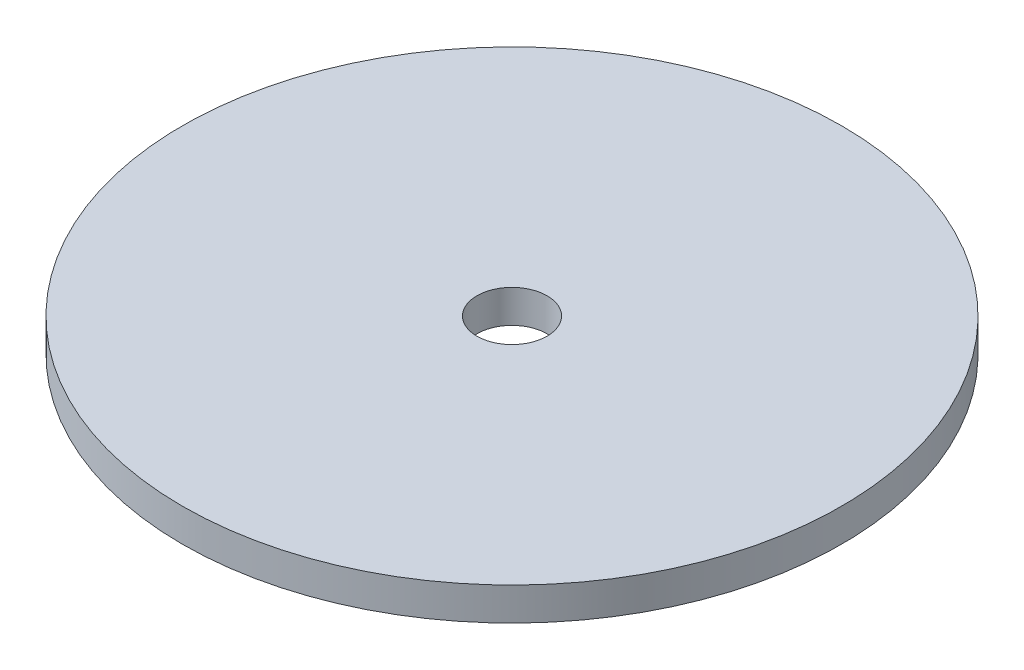
SolidWorks part; units mm, degrees
ref_plane "Front Plane" through (0, 0, 0) normal (0, 0, 1) x (1, 0, 0)
ref_plane "Top Plane" through (0, 0, 0) normal (0, 1, 0) x (1, 0, 0)
ref_plane "Right Plane" through (0, 0, 0) normal (1, 0, 0) x (0, 0, -1)
sketch "Sketch1" plane through (0, 0, 0) normal (0, 1, 0) x (1, 0, 0)
  circle A0 centre (0, 0) radius 31.75
  dimension "D1" = 63.5
extrude "Boss-Extrude1" add sketch "Sketch1" along normal mid plane 3.175
sketch "Sketch2" plane through (0, 1.5875, 0) normal (0, 1, 0) x (1, 0, 0)
  circle A2 centre (0, 0) radius 3.3782
  point P1 (-13.3296, -1.7258)
  dimension "D1" = 6.7564
extrude "Cut-Extrude1" cut sketch "Sketch2" against normal through all
